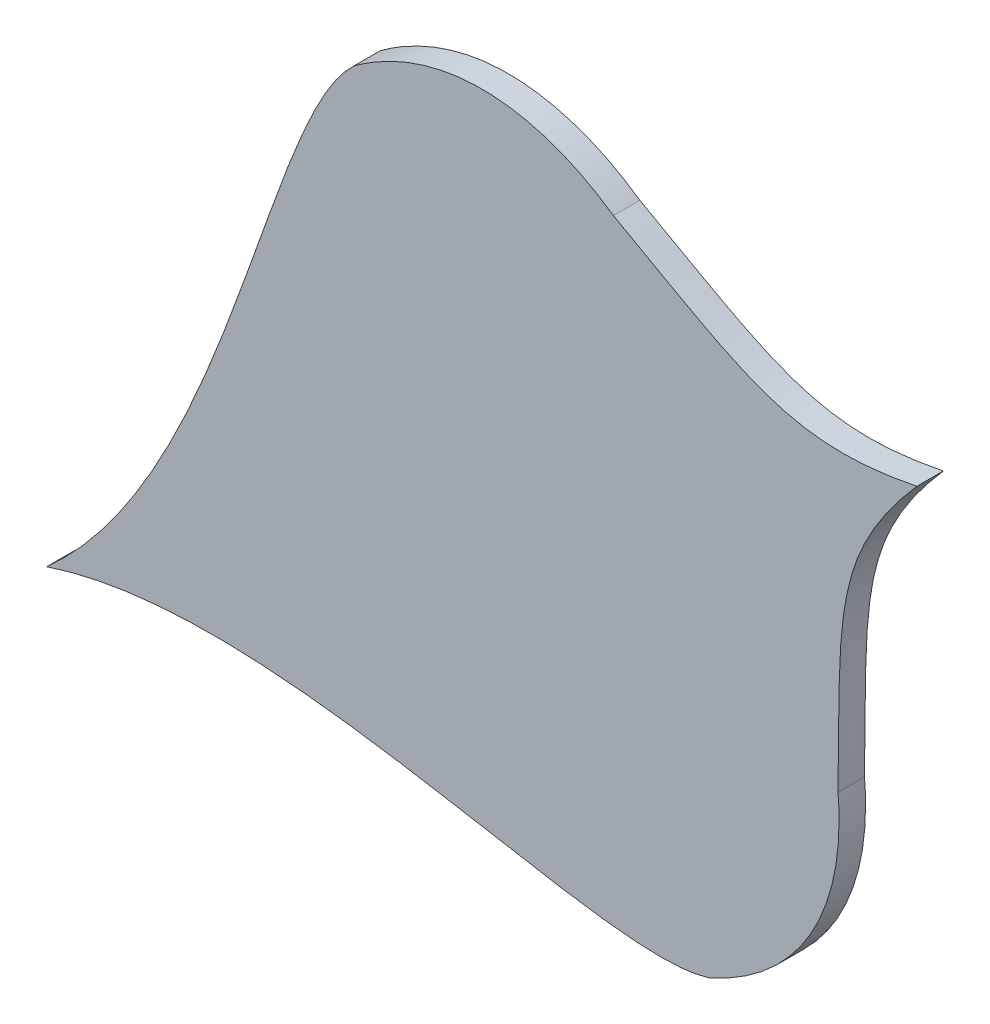
SolidWorks part; units mm, degrees
ref_plane "Front Plane" through (0, 0, 0) normal (0, 0, 1) x (1, 0, 0)
ref_plane "Top Plane" through (0, 0, 0) normal (0, 1, 0) x (1, 0, 0)
ref_plane "Right Plane" through (0, 0, 0) normal (1, 0, 0) x (0, 0, -1)
sketch "Sketch1" plane through (0, 0, 0) normal (0, 0, 1) x (1, 0, 0)
  line L0 (318.6667, 759.5) -> (1593.3333, 759.5) construction
  line L1 (1664.6673, 1175.413) -> (200.8708, 326.3795) construction
  spline S0 degree 3 poles (1415.7694, 1031.0468) (1367.6282, 1021.3391) (1351.5457, 1034.491) (1301.2172, 1062.2812) knots 0 0 0 0 1 1 1 1
  spline S1 degree 3 poles (1301.2172, 1062.2812) (1274.4855, 1081.0177) (1237.9229, 1087.5407) (1203.2848, 1062.2883) knots 0 0 0 0 1 1 1 1
  spline S2 degree 3 poles (1203.2848, 1062.2883) (1170.1984, 1031.5989) (1156.257, 901.987) (1087.2493, 840.4982) knots 0 0 0 0 1 1 1 1
  spline S3 degree 3 poles (1415.7694, 1031.0468) (1383.4393, 994.0795) (1386.87, 973.5893) (1386.0028, 916.1045) knots 0 0 0 0 1 1 1 1
  spline S4 degree 3 poles (1386.0028, 916.1045) (1388.9933, 883.5976) (1376.501, 848.6218) (1337.3826, 831.0937) knots 0 0 0 0 1 1 1 1
  spline S5 degree 3 poles (1337.3826, 831.0937) (1294.3152, 817.6123) (1174.8872, 869.8671) (1087.2493, 840.4982) knots 0 0 0 0 1 1 1 1
extrude "Boss-Extrude1" add sketch "Sketch1" along normal blind 10
